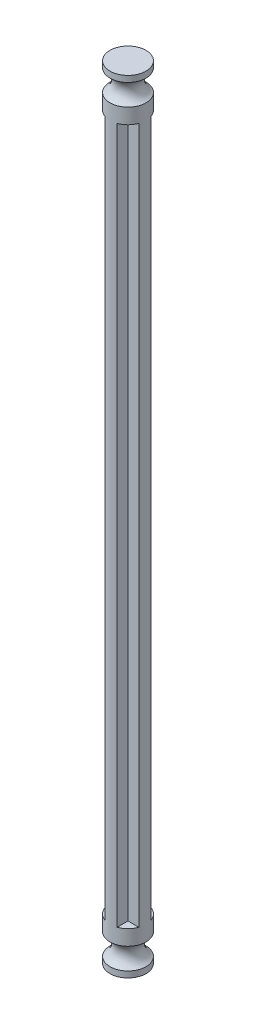
SolidWorks part; units mm, degrees
ref_plane "前视基准面" through (0, 0, 0) normal (0, 0, 1) x (1, 0, 0)
ref_plane "上视基准面" through (0, 0, 0) normal (0, 1, 0) x (1, 0, 0)
ref_plane "右视基准面" through (0, 0, 0) normal (1, 0, 0) x (0, 0, -1)
sketch "草图1" plane through (0, 0, 0) normal (0, 1, 0) x (1, 0, 0)
  line L0 (1, 1) -> (1, 2.7753)
  line L7 (1, 1) -> (2.7753, 1)
  line L8 (1, -1) -> (2.7753, -1)
  line L9 (1, -1) -> (1, -2.7753)
  line L10 (-1, -1) -> (-1, -2.7753)
  line L11 (-1, -1) -> (-2.7753, -1)
  line L12 (-1, 1) -> (-2.7753, 1)
  line L13 (-1, 1) -> (-1, 2.7753)
  arc A0 (-2.7753, 1) -> (-2.7753, -1) centre (0, 0) ccw
  arc A1 (-1, -2.7753) -> (1, -2.7753) centre (0, 0) ccw
  arc A2 (2.7753, -1) -> (2.7753, 1) centre (0, 0) ccw
  arc A3 (1, 2.7753) -> (-1, 2.7753) centre (0, 0) ccw
  dimension "D1" = 5.9
  dimension "D2" = 2
  dimension "D3" = 2
  dimension "D4" = 2
  dimension "D5" = 2
  dimension "D6" = 1
  dimension "D7" = 1
  dimension "D8" = 1
  dimension "D9" = 1
extrude "凸台-拉伸2" add sketch "草图1" along normal blind 114
sketch "草图3" plane through (0, 0, 0) normal (1, 0, 0) x (0, 0, -1)
  line L0 (0, 114) -> (0, 121)
  line L1 (1, 114) -> (-1, 114) construction
  line L2 (0, 121) -> (2.95, 121)
  line L3 (0, 114) -> (2.95, 114)
  line L4 (2.95, 114) -> (2.95, 116.5)
  line L5 (2.95, 121) -> (2.95, 120)
  line L6 (0, 0) -> (0, -7)
  line L7 (0, -7) -> (2.95, -7)
  line L8 (0, 0) -> (2.95, 0)
  line L9 (2.95, 0) -> (2.95, -2.5)
  line L10 (2.95, -7) -> (2.95, -6)
  arc A0 (2.95, 120) -> (2.95, 116.5) centre (3.9182, 118.25) ccw
  arc A1 (2.95, -2.5) -> (2.95, -6) centre (3.9182, -4.25) ccw
  dimension "D5" = 1
  dimension "D4" = 2
  dimension "D9" = 2
  dimension "D1" = 2.95
  dimension "D2" = 7
  dimension "D3" = 2.5
  dimension "D6" = 7
  dimension "D7" = 2.5
  dimension "D8" = 1
revolve "旋转3" add sketch "草图3" angle 360 about L6
